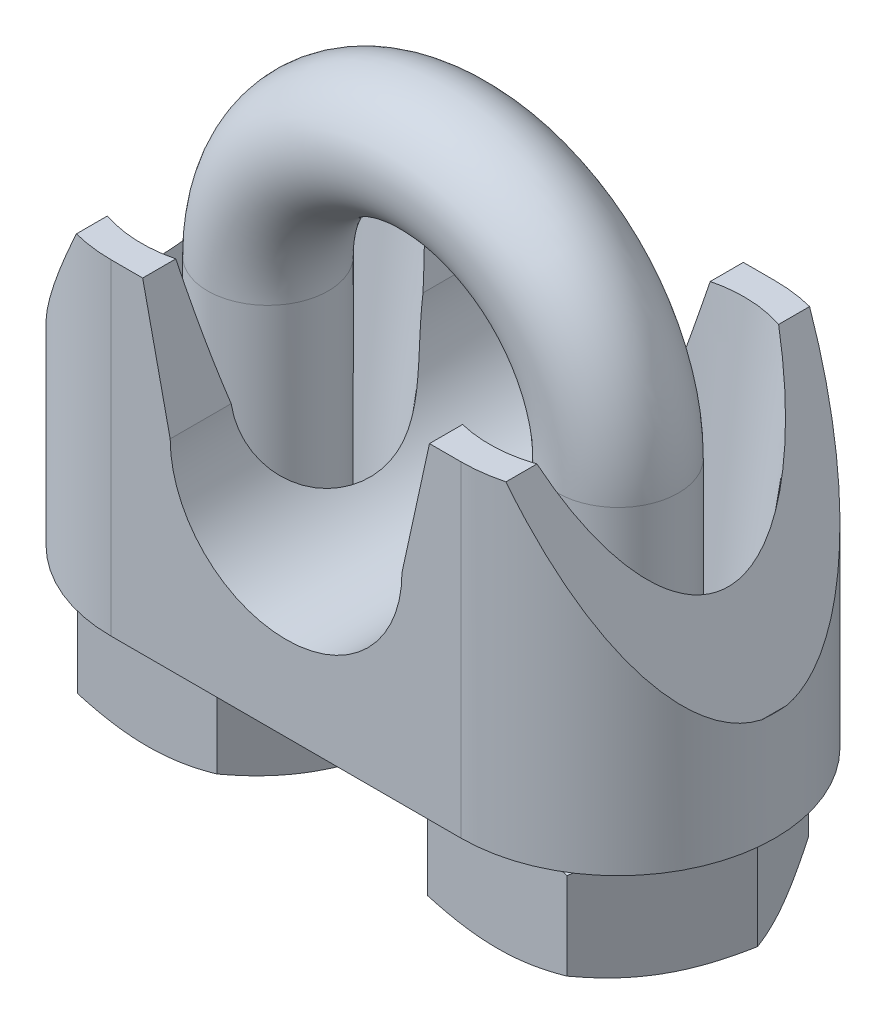
SolidWorks part; units mm, degrees
ref_plane "Front Plane" through (0, 0, 0) normal (0, 0, 1) x (1, 0, 0)
ref_plane "Top Plane" through (0, 0, 0) normal (0, 1, 0) x (1, 0, 0)
ref_plane "Right Plane" through (0, 0, 0) normal (1, 0, 0) x (0, 0, -1)
sketch "Sketch1" plane through (0, 0, 0) normal (0, 1, 0) x (1, 0, 0)
  line L0 (0, 0) -> (14.5, 0) construction
  line L1 (0, 6.5) -> (14.5, 6.5)
  line L2 (0, -6.5) -> (14.5, -6.5)
  arc A0 (0, 6.5) -> (0, -6.5) centre (0, 0) ccw
  arc A1 (14.5, -6.5) -> (14.5, 6.5) centre (14.5, 0) ccw
  point P3 (7.25, 0)
  dimension "D1" = 27.5
  dimension "D2" = 13
extrude "Boss-Extrude1" add sketch "Sketch1" along normal blind 13.5
sketch "Sketch2" plane through (0, 0, 0) normal (0, -1, 0) x (1, 0, 0)
  circle A0 centre (14.455, 0) radius 3.625
  circle A1 centre (0.045, 0) radius 3.625
  arc A3 (0, 6.5) -> (0, -6.5) centre (0, 0) ccw construction
  arc A4 (14.5, -6.5) -> (14.5, 6.5) centre (14.5, 0) ccw construction
  point P4 (0, 0)
  point P9 (-6.5, 0)
  dimension "D1" = 7.25
  dimension "D2" = 2.92
  dimension "D3" = 2.92
extrude "Cut-Extrude1" cut sketch "Sketch2" against normal through all draft 7 draft outward yes
sketch "Sketch3" plane through (0, 0, 6.5) normal (0, 0, 1) x (1, 0, 0)
  line L0 (0, 13.5) -> (14.5, 13.5) construction
  line L5 (2.45, 8.3) -> (1.3106, 13.5)
  line L6 (1.3106, 13.5) -> (13.1894, 13.5)
  line L7 (0, 0) -> (14.5, 0) construction
  line L8 (12.05, 8.3) -> (13.1894, 13.5)
  line L9 (7.25, 13.5) -> (7.25, 0) construction
  arc A0 (2.45, 8.3) -> (12.05, 8.3) centre (7.25, 8.3) ccw
  point P0 (7.25, 13.5)
  dimension "D2" = 3.5
  dimension "D1" = 9.6
extrude "Cut-Extrude2" cut sketch "Sketch3" against normal through all
sketch "Sketch5" plane through (0, 0, 0) normal (0, 0, 1) x (1, 0, 0)
  line L0 (14.455, 0) -> (14.455, 33.2959) construction
  line L1 (10.83, 0) -> (18.08, 0) construction
  line L2 (14.455, 16.6479) -> (20.9791, 4.5)
  line L5 (21.1799, 16.6479) -> (14.455, 16.6479)
  line L7 (14.5, 0) -> (21, 0) construction
  line L8 (21.1799, 16.6479) -> (22.8324, 16.6479)
  line L9 (22.8324, 16.6479) -> (22.8324, 4.5)
  line L10 (22.8324, 4.5) -> (20.9791, 4.5)
  line L11 (21, 13.5) -> (14.5, 13.5) construction
  line L12 (7.25, 0) -> (7.25, 13.5237) construction
  line L13 (0, 0) -> (14.5, 0) construction
  line L14 (-8.3324, 4.5) -> (-6.4791, 4.5)
  line L15 (-8.3324, 16.6479) -> (-8.3324, 4.5)
  line L16 (-6.6799, 16.6479) -> (-8.3324, 16.6479)
  line L17 (-6.6799, 16.6479) -> (0.045, 16.6479)
  line L18 (0.045, 16.6479) -> (-6.4791, 4.5)
  dimension "D1" = 4.5
  dimension "D2" = 3.1479
extrude "Cut-Extrude5" cut sketch "Sketch5" against normal mid plane 34
sketch "Sketch6" plane through (0, 0, 0) normal (0, 0, 1) x (1, 0, 0)
  line L0 (14.5, 0) -> (14.5, 10.38)
  line L1 (0, 0) -> (0, 10.38)
  line L2 (14.5, 0) -> (14.5, -4.7)
  line L3 (10.83, 0) -> (18.08, 0) construction
  line L4 (0, 0) -> (0, -4.7)
  line L5 (14.5, 0) -> (21, 0) construction
  arc A0 (14.5, 10.38) -> (0, 10.38) centre (7.25, 10.38) ccw
  point P7 (0, 0)
  dimension "D1" = 17.63
  dimension "D2" = 4.7
sweep "Sweep1" add path "Sketch6" circular profile diameter 5 parameters "D3"=5
sketch "Sketch35" plane through (0, -4.7, 0) normal (0, -1, 0) x (1, 0, 0)
  line L0 (7.25, 6.5) -> (7.25, -6.5) construction
  line L1 (11.6132, -5) -> (17.3868, -5)
  line L2 (17.3868, -5) -> (20.2735, 0)
  line L3 (20.2735, 0) -> (17.3868, 5)
  line L4 (17.3868, 5) -> (11.6132, 5)
  line L5 (11.6132, 5) -> (8.7265, 0)
  line L6 (8.7265, 0) -> (11.6132, -5)
  line L7 (0, 6.5) -> (14.5, 6.5) construction
  line L8 (14.5, -6.5) -> (0, -6.5) construction
  line L9 (5.7735, 0) -> (2.8868, -5)
  line L10 (2.8868, 5) -> (5.7735, 0)
  line L11 (-2.8868, 5) -> (2.8868, 5)
  line L12 (-5.7735, 0) -> (-2.8868, 5)
  line L13 (-2.8868, -5) -> (-5.7735, 0)
  line L14 (2.8868, -5) -> (-2.8868, -5)
  circle A0 centre (14.5, 0) radius 5 construction
  circle A1 centre (0, 0) radius 5 construction
  dimension "D1" = 10
extrude "Boss-Extrude2" add sketch "Sketch35" against normal blind 4.5
sketch "Sketch36" plane through (0, 0, 0) normal (1, 0, 0) x (0, 0, -1)
  line L0 (0, 0) -> (0, -7.0279) construction
  line L1 (-6.5, 0) -> (6.5, 0) construction
  line L2 (5, -0.2) -> (7.1507, -1.4417)
  line L3 (5, -4.7) -> (7.3139, -4.7)
  line L6 (7.3139, -4.7) -> (7.3139, -3.364)
  line L7 (5, -0.2) -> (7.1507, -0.2)
  line L10 (7.1507, -0.2) -> (7.1507, -1.4417)
  line L11 (5, -4.7) -> (7.3139, -3.364)
  dimension "D1" = 30
  dimension "D2" = 30
revolve "Cut-Revolve2" cut sketch "Sketch36" angle 360 about L0
ref_plane "Plane1" through (7.25, 0, 0) normal (-1, 0, 0) x (0, 0, 1)
mirror "Mirror1" about plane through (7.25, 0, 0) normal (-1, 0, 0) of "Cut-Revolve2"
